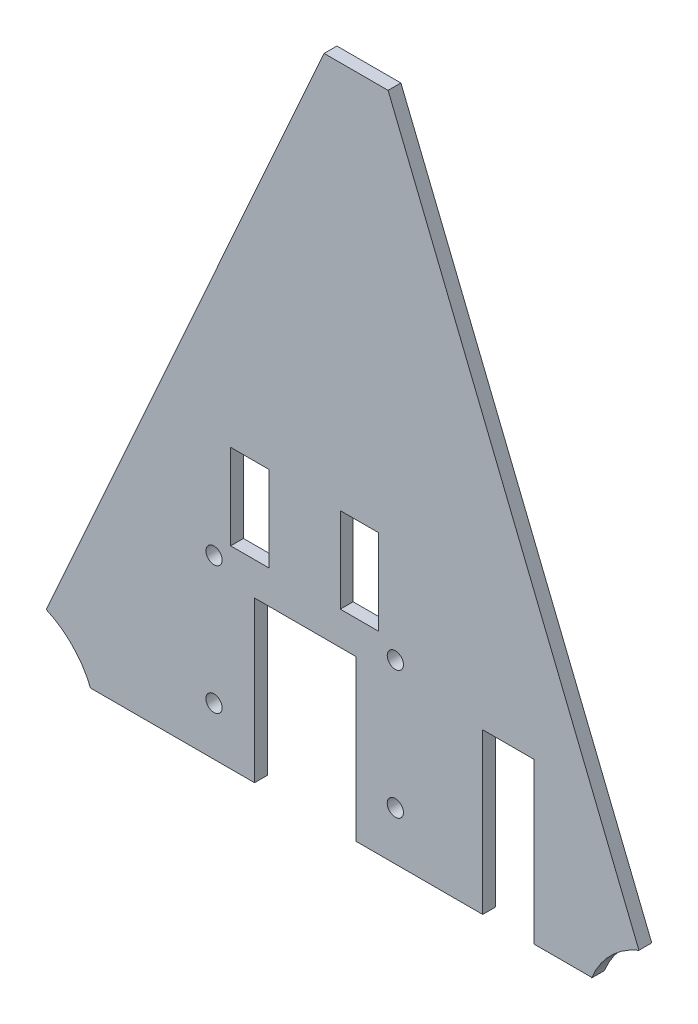
SolidWorks part; units mm, degrees
ref_plane "Front Plane" through (0, 0, 0) normal (0, 0, 1) x (1, 0, 0)
ref_plane "Top Plane" through (0, 0, 0) normal (0, 1, 0) x (1, 0, 0)
ref_plane "Right Plane" through (0, 0, 0) normal (1, 0, 0) x (0, 0, -1)
sketch "Sketch2" plane through (0, 0, 0) normal (0, 0, 1) x (1, 0, 0)
  line L0 (-189.7401, 245.3834) -> (-375.9085, -170.4146)
  line L1 (-375.9085, -170.4146) -> (16.7755, -170.4146)
  line L2 (16.7755, -170.4146) -> (-151.6401, 245.3834)
  line L4 (-189.7401, 245.3834) -> (-151.6401, 245.3834)
  point P2 (0, 0)
  dimension "D1" = 415.798
  dimension "D2" = 415.798
  dimension "D3" = 67.95
  dimension "D4" = 38.1
  dimension "D5" = 392.684
extrude "Boss-Extrude1" add sketch "Sketch2" along normal blind 7.62 contours L0 L1 L2 L4
sketch "Sketch5" plane through (0, 0, 0) normal (0, 0, -1) x (-1, 0, 0)
  circle A0 centre (375.9085, -170.4146) radius 15.875
  dimension "D1" = 31.75
extrude "Cut-Extrude2" cut sketch "Sketch5" against normal blind 50.8
sketch "Sketch6" plane through (0, 0, 0) normal (0, 0, -1) x (-1, 0, 0)
  circle A0 centre (-16.7755, -170.4146) radius 15.875
  dimension "D1" = 31.75
extrude "Cut-Extrude3" cut sketch "Sketch6" against normal blind 50.8 contours A0
ref_plane "Plane1" through (-360.0335, -170.4146, 0) normal (1, 0, 0) x (0, 0, -1)
sketch "Sketch8" plane through (0, 0, 0) normal (0, 0, -1) x (-1, 0, 0)
  line L0 (254.9716, -43.4146) -> (147.0216, -43.4146) construction
  line L1 (360.0335, -170.4146) -> (-0.9005, -170.4146) construction
  line L2 (254.9716, -170.4146) -> (254.9716, 97.7332) construction
  line L3 (254.9716, -43.4146) -> (254.9716, -170.4146) construction
  line L4 (147.0216, -43.4146) -> (147.0216, -170.4146) construction
  line L5 (147.0216, -170.4146) -> (183.5239, -170.4146) construction
  line L6 (183.5239, -170.4146) -> (183.5239, -56.1146) construction
  line L7 (170.6901, 245.3834) -> (179.5665, -170.4146) construction
  line L8 (189.7401, 245.3834) -> (151.6401, 245.3834) construction
  line L9 (183.5239, -56.1146) -> (218.4489, -56.1146) construction
  line L10 (218.4489, -56.1146) -> (218.4489, -170.4146) construction
  line L11 (218.4489, -170.4146) -> (218.4489, -56.1146)
  line L12 (218.4489, -56.1146) -> (183.5239, -56.1146)
  line L13 (183.5239, -56.1146) -> (183.5239, -170.4146)
  line L14 (183.5239, -109.7533) -> (7.7949, -109.7533) construction
  line L15 (-10.8158, -155.7008) -> (151.6401, 245.3834) construction
  line L16 (7.7949, -109.7533) -> (7.7949, -170.4146) construction
  dimension "D1" = 268.1478
  dimension "D2" = 107.95
  dimension "D3" = 127
  dimension "D4" = 36.5023
  dimension "D5" = 114.3
  dimension "D6" = 34.925
  dimension "D7" = 175.7291
  dimension "D8" = 60.6613
extrude "Cut-Extrude4" cut sketch "Sketch8" against normal blind 7.62 and the other way through all contours L11 L12 L13
sketch "Sketch9" plane through (0, 0, 0) normal (0, 0, -1) x (-1, 0, 0)
  line L0 (152.1549, -122.4086) -> (183.5239, -122.4086) construction
  line L1 (183.5239, -170.4146) -> (183.5239, -56.1146) construction
  line L2 (147.3289, -127.2346) -> (147.3289, -170.4146) construction
  line L3 (183.5239, -170.4146) -> (-0.9005, -170.4146) construction
  line L4 (250.4529, -122.4086) -> (218.4489, -122.4086) construction
  line L5 (218.4489, -56.1146) -> (218.4489, -170.4146) construction
  line L6 (255.2789, -127.2346) -> (255.2789, -170.4146) construction
  line L7 (360.0335, -170.4146) -> (218.4489, -170.4146) construction
  circle A0 centre (147.3289, -122.4086) radius 4.826
  circle A1 centre (255.2789, -122.4086) radius 4.826
  dimension "D3" = 9.652
  dimension "D6" = 9.652
  dimension "D1" = 31.369
  dimension "D2" = 43.18
  dimension "D4" = 32.004
  dimension "D5" = 43.18
sketch "Sketch10" plane through (0, 0, 0) normal (0, 0, -1) x (-1, 0, 0)
  line L0 (218.4489, -110.7541) -> (349.1963, -110.7541) construction
  line L1 (218.4489, -56.1146) -> (218.4489, -170.4146) construction
  line L2 (189.7401, 245.3834) -> (369.4213, -155.9256) construction
  line L3 (7.3895, -110.7541) -> (138.1995, -110.7541) construction
  line L4 (-10.8158, -155.7008) -> (151.6401, 245.3834) construction
  line L5 (64.8263, -170.4146) -> (64.8263, -56.1146) construction
  line L8 (183.5239, -170.4146) -> (-0.9005, -170.4146) construction
  line L9 (64.8263, -56.1146) -> (95.3063, -56.1146) construction
  line L11 (95.3063, -56.1146) -> (95.3063, -170.4146) construction
  line L12 (64.8263, -170.4146) -> (64.8263, -56.1146)
  line L13 (64.8263, -56.1146) -> (95.3063, -56.1146)
  line L14 (95.3063, -56.1146) -> (95.3063, -170.4146)
  line L15 (64.8263, -170.4146) -> (95.3063, -170.4146)
  dimension "D1" = 130.7473
  dimension "D2" = 130.81
  dimension "D3" = 114.3
  dimension "D4" = 30.48
extrude "Cut-Extrude6" cut sketch "Sketch9" against normal up to next
extrude "Cut-Extrude12" cut sketch "Sketch10" against normal blind 25.4 contours L13 L14 L15 L12
sketch "Sketch14" plane through (0, 0, 0) normal (0, 0, -1) x (-1, 0, 0)
  circle A0 centre (-16.7755, -170.4146) radius 50.8
  dimension "D1" = 101.6
extrude "Cut-Extrude14" cut sketch "Sketch14" against normal up to next
sketch "Sketch15" plane through (0, 0, 0) normal (0, 0, -1) x (-1, 0, 0)
  circle A0 centre (375.9085, -170.4146) radius 50.8
  dimension "D1" = 101.6
extrude "Cut-Extrude15" cut sketch "Sketch15" against normal up to next
sketch "Sketch18" plane through (0, 0, 0) normal (0, 0, -1) x (-1, 0, 0)
  line L0 (0, 0) -> (30.4451, 0) construction
  line L5 (30.4451, -170.4146) -> (331.0546, -170.4146)
  line L6 (30.4451, -170.4146) -> (30.4451, -151.3646)
  line L7 (30.4451, -151.3646) -> (331.0546, -151.3646)
  line L8 (331.0546, -170.4146) -> (331.0546, -151.3646)
  line L9 (30.4451, 0) -> (30.4451, -151.3646) construction
  point P8 (0, 0)
  dimension "D1" = 19.05
  dimension "D2" = 30.4451
  dimension "D3" = 151.3646
  dimension "D4" = 300.6095
extrude "Cut-Extrude17" cut sketch "Sketch18" against normal up to next contours L7 L8 L5 L6
sketch "Sketch19" plane through (0, 0, 0) normal (0, 0, -1) x (-1, 0, 0)
  line L0 (255.2789, -122.4086) -> (255.2789, -46.2086) construction
  line L1 (147.3289, -122.4086) -> (147.3289, -46.2086) construction
  circle A0 centre (255.2789, -46.2086) radius 4.826
  circle A1 centre (147.3289, -46.2086) radius 4.826
  dimension "D3" = 9.652
  dimension "D4" = 9.652
  dimension "D1" = 76.2
  dimension "D2" = 76.2
extrude "Cut-Extrude18" cut sketch "Sketch19" against normal up to next
sketch "Sketch20" plane through (0, 0, 0) normal (0, 0, -1) x (-1, 0, 0)
  line L0 (152.1549, -46.2086) -> (253.7549, -46.2086) construction
  line L5 (253.7549, -46.2086) -> (253.7549, -28.5286) construction
  line L6 (147.3289, -46.2086) -> (147.3289, 23.5628) construction
  line L7 (157.2349, 14.4658) -> (180.0949, 14.4658)
  line L8 (157.2349, 14.4658) -> (157.2349, -36.3342)
  line L9 (157.2349, -36.3342) -> (180.0949, -36.3342)
  line L10 (180.0949, 14.4658) -> (180.0949, -36.3342)
  line L11 (157.2349, -10.9342) -> (147.3289, -10.9342) construction
  line L12 (255.2789, -46.2086) -> (255.2789, 23.5628) construction
  line L13 (222.5129, 14.4658) -> (245.3729, 14.4658)
  line L14 (222.5129, 14.4658) -> (222.5129, -36.3342)
  line L15 (222.5129, -36.3342) -> (245.3729, -36.3342)
  line L16 (245.3729, 14.4658) -> (245.3729, -36.3342)
  line L17 (245.3729, -10.9342) -> (255.2789, -10.9342) construction
  line L18 (168.6649, -36.3342) -> (168.6649, -46.2086) construction
  line L19 (233.9429, -36.3342) -> (233.9429, -46.2086) construction
  circle A0 centre (147.3289, -46.2086) radius 4.826 construction
  dimension "D1" = 22.86
  dimension "D2" = 50.8
  dimension "D3" = 101.6
  dimension "D4" = 9.906
  dimension "D5" = 22.86
  dimension "D6" = 50.8
  dimension "D7" = 9.906
  dimension "D8" = 9.8744
extrude "Cut-Extrude19" cut sketch "Sketch20" against normal up to next contours L14 L15 L16 L13 | L10 L9 L8 L7
sketch "Sketch21" plane through (0, 0, 0) normal (0, 0, -1) x (-1, 0, 0)
  line L1 (218.4489, -151.3646) -> (231.1489, -151.3646)
  line L2 (218.4489, -151.3646) -> (218.4489, -56.1146)
  line L3 (218.4489, -56.1146) -> (231.1489, -56.1146)
  line L4 (231.1489, -151.3646) -> (231.1489, -56.1146)
  line L5 (183.5239, -151.3646) -> (170.8239, -151.3646)
  line L6 (183.5239, -151.3646) -> (183.5239, -56.1146)
  line L7 (183.5239, -56.1146) -> (170.8239, -56.1146)
  line L8 (170.8239, -151.3646) -> (170.8239, -56.1146)
  dimension "D1" = 12.7
  dimension "D2" = 95.25
  dimension "D3" = 12.7
  dimension "D4" = 95.25
extrude "Cut-Extrude20" cut sketch "Sketch21" against normal up to next contours L4 L3 L2 L1 | L8 L7 L6 L5
